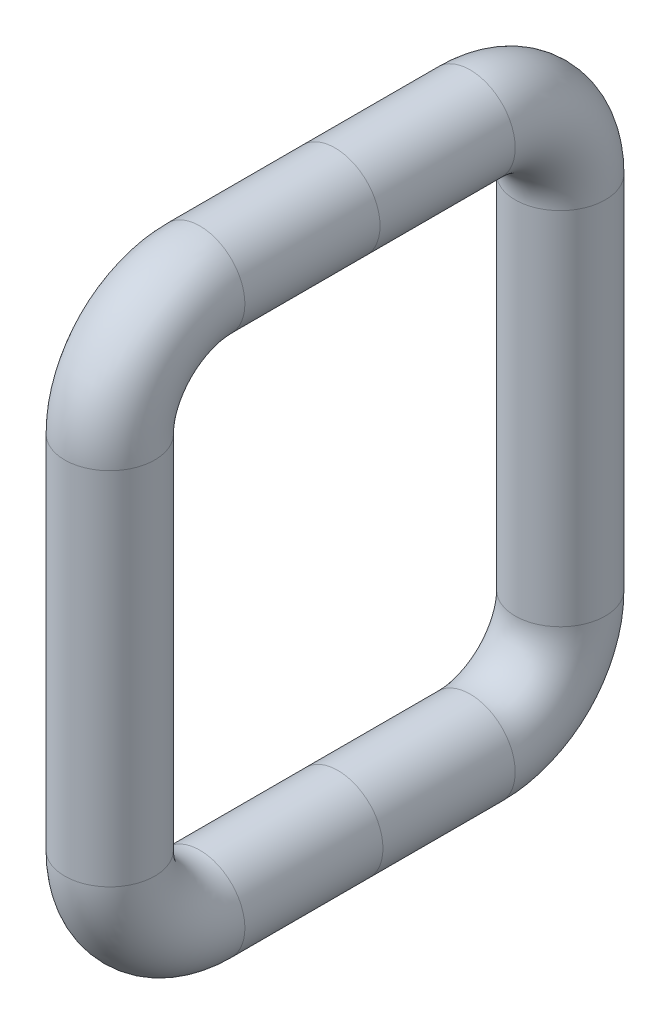
SolidWorks part; units mm, degrees
ref_plane "Front Plane" through (0, 0, 0) normal (0, 0, 1) x (1, 0, 0)
ref_plane "Top Plane" through (0, 0, 0) normal (0, 1, 0) x (1, 0, 0)
ref_plane "Right Plane" through (0, 0, 0) normal (1, 0, 0) x (0, 0, -1)
sketch "Sketch1" plane through (0, 0, 0) normal (0, 0, 1) x (1, 0, 0)
  circle A0 centre (0, 36.9686) radius 25.4
sketch3d "3DSketch1"
  line L0 (0, 36.9686, 0) -> (0, 36.9686, -76.2)
  line L1 (0, -13.8314, -127) -> (0, -217.0314, -127)
  line L2 (0, -267.8314, -76.2) -> (0, -267.8314, -1.6391)
  line L3 (0, -267.8314, -1.6391) -> (0, -267.8314, 76.2)
  line L4 (0, -217.0314, 127) -> (0, -13.8314, 127)
  line L5 (0, 36.9686, 0) -> (0, 36.9686, 76.2)
  arc A0 (0, 36.9686, -76.2) -> (0, -13.8314, -127) centre (0, -13.8314, -76.2) ccw
  arc A1 (0, -217.0314, -127) -> (0, -267.8314, -76.2) centre (0, -217.0314, -76.2) ccw
  arc A2 (0, -267.8314, 76.2) -> (0, -217.0314, 127) centre (0, -217.0314, 76.2) ccw
  arc A3 (0, 36.9686, 76.2) -> (0, -13.8314, 127) centre (0, -13.8314, 76.2) ccw
  point P9 (0, 36.9686, -127)
  point P10 (-50.8, -13.8314, -76.2)
  point P13 (0, -267.8314, -127)
  point P14 (-50.8, -217.0314, -76.2)
  point P17 (0, -267.8314, 127)
  point P18 (-50.8, -217.0314, 76.2)
  point P21 (0, 36.9686, 127)
  point P22 (50.8, -13.8314, 76.2)
  dimension "D3" = 50.8
  dimension "D1" = 127
  dimension "D2" = 304.8
sweep "Sweep1" add profiles "Sketch1" path "3DSketch1"
